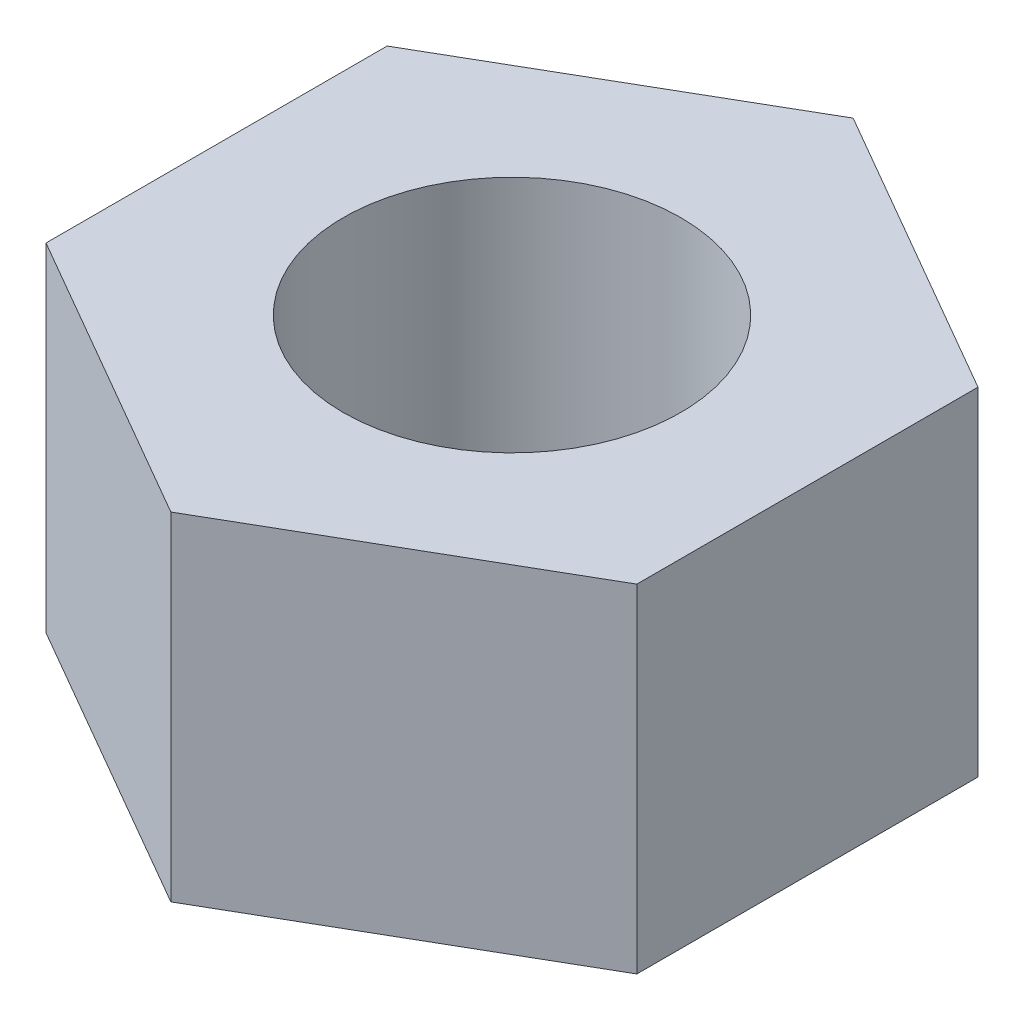
SolidWorks part; units mm, degrees
ref_plane "Front Plane" through (0, 0, 0) normal (0, 0, 1) x (1, 0, 0)
ref_plane "Top Plane" through (0, 0, 0) normal (0, 1, 0) x (1, 0, 0)
ref_plane "Right Plane" through (0, 0, 0) normal (1, 0, 0) x (0, 0, -1)
sketch "Sketch1" plane through (0, 0, 0) normal (0, 1, 0) x (1, 0, 0)
  line L1 (0, -4.0415) -> (3.5, -2.0207)
  line L2 (3.5, -2.0207) -> (3.5, 2.0207)
  line L3 (3.5, 2.0207) -> (0, 4.0415)
  line L4 (0, 4.0415) -> (-3.5, 2.0207)
  line L5 (-3.5, 2.0207) -> (-3.5, -2.0207)
  line L6 (-3.5, -2.0207) -> (0, -4.0415)
  circle A0 centre (0, 0) radius 3.5 construction
  circle A1 centre (0, 0) radius 2
  dimension "D2" = 4
  dimension "D1" = 7
extrude "Boss-Extrude1" add sketch "Sketch1" along normal blind 4
